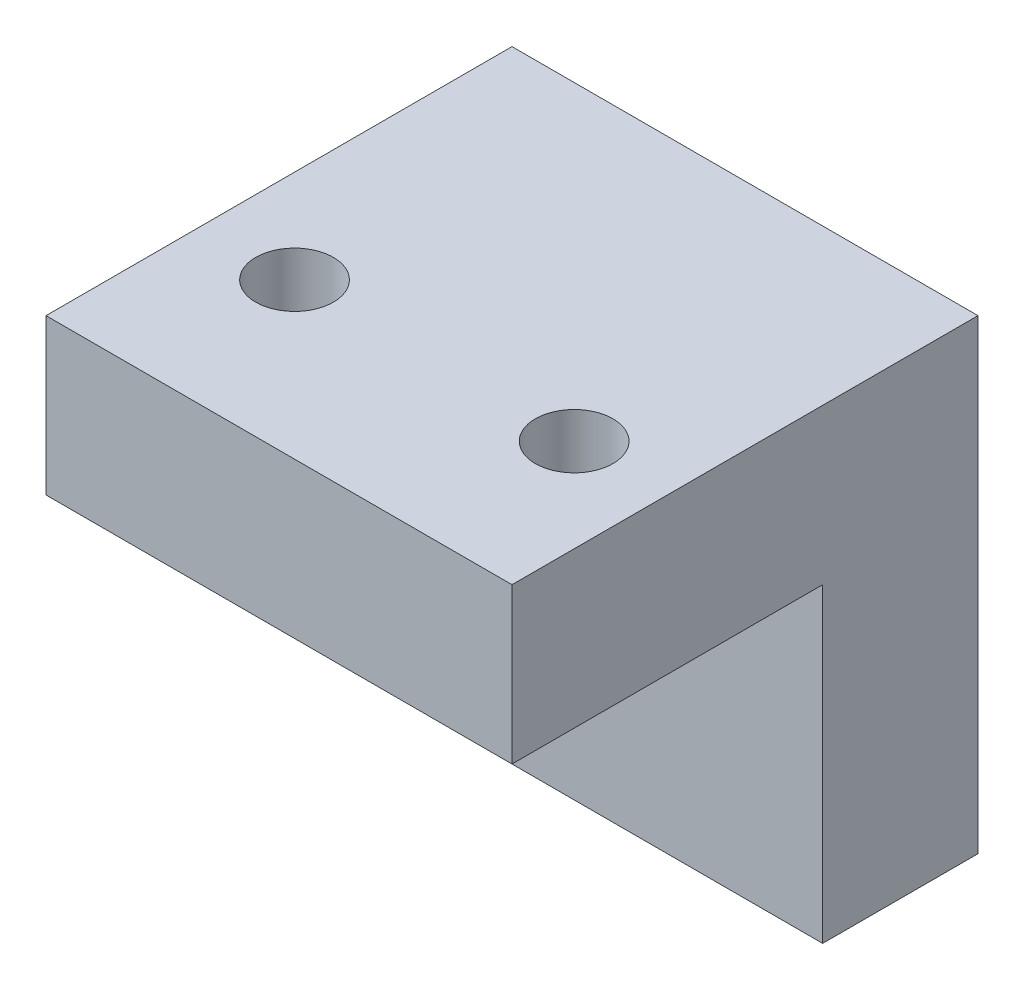
SolidWorks part; units mm, degrees
material "1060 合金"
ref_plane "前视基准面" through (0, 0, 0) normal (0, 0, 1) x (1, 0, 0)
ref_plane "上视基准面" through (0, 0, 0) normal (0, 1, 0) x (1, 0, 0)
ref_plane "右视基准面" through (0, 0, 0) normal (1, 0, 0) x (0, 0, -1)
sketch "草图1" plane through (0, 0, 0) normal (0, 1, 0) x (1, 0, 0)
  line L1 (0, 0) -> (15, 0)
  line L2 (0, 0) -> (0, 5)
  line L3 (0, 5) -> (15, 5)
  line L4 (15, 0) -> (15, 5)
  dimension "D1" = 5
  dimension "D2" = 15
extrude "凸台-拉伸1" add sketch "草图1" along normal blind 10
sketch "草图2" plane through (0, 10, 0) normal (0, 1, 0) x (1, 0, 0)
  line L0 (15, 0) -> (15, 5) construction
  line L1 (0, 5) -> (15, 5)
  line L2 (0, 5) -> (0, -10)
  line L3 (0, -10) -> (15, -10)
  line L4 (15, 5) -> (15, -10)
  dimension "D1" = 15
extrude "凸台-拉伸2" add sketch "草图2" along normal blind 5
sketch "草图3" plane through (0, 0, 0) normal (0, 0, 1) x (1, 0, 0)
  line L0 (7.5, 0) -> (7.5, 10) construction
  line L1 (0, 0) -> (15, 0) construction
  line L2 (0, 10) -> (15, 10) construction
  circle A3 centre (7.5, 5) radius 1.25
  dimension "D1" = 5
  dimension "D2" = 2.5
extrude "切除-拉伸1" cut sketch "草图3" against normal through all
sketch "草图4" plane through (0, 15, 0) normal (0, 1, 0) x (1, 0, 0)
  line L0 (0, -10) -> (15, -10) construction
  line L1 (0, 5) -> (0, -10) construction
  circle A2 centre (3, -5) radius 1.25
  circle A3 centre (12, -5) radius 1.25
  dimension "D1" = 9
  dimension "D2" = 5
  dimension "D4" = 2.5
  dimension "D3" = 3
extrude "切除-拉伸2" cut sketch "草图4" against normal blind 5
